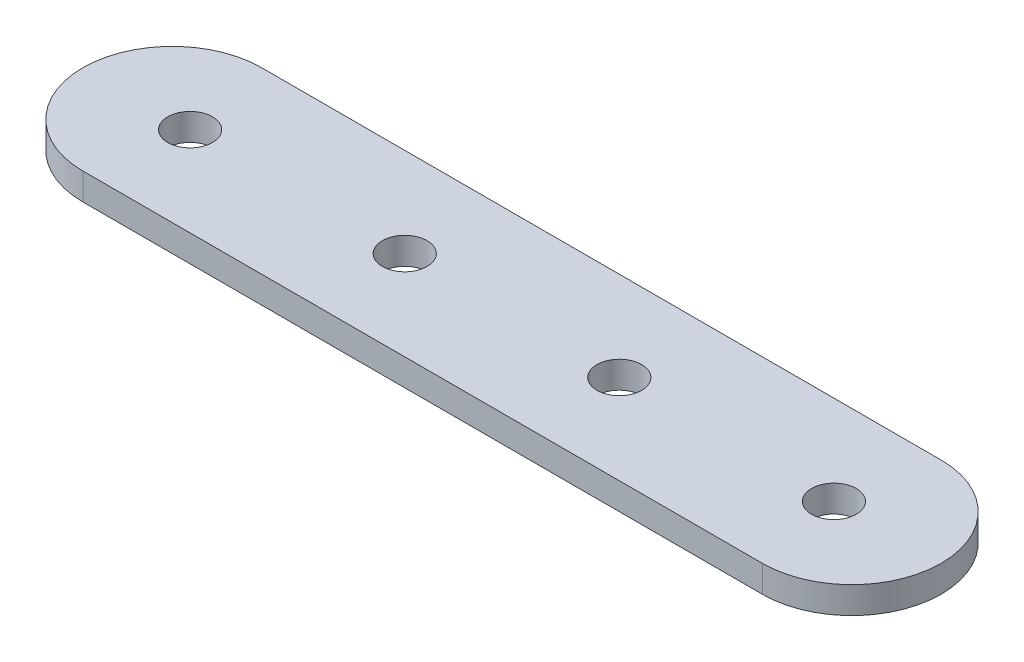
SolidWorks part; units mm, degrees
ref_plane "前视基准面" through (0, 0, 0) normal (0, 0, 1) x (1, 0, 0)
ref_plane "上视基准面" through (0, 0, 0) normal (0, 1, 0) x (1, 0, 0)
ref_plane "右视基准面" through (0, 0, 0) normal (1, 0, 0) x (0, 0, -1)
sketch "草图1" plane through (0, 0, 0) normal (0, 1, 0) x (1, 0, 0)
  line L0 (10, 0) -> (86, 0)
  line L2 (86, 20) -> (10, 20)
  arc A0 (10, 20) -> (10, 0) centre (10, 10) ccw
  arc A1 (86, 0) -> (86, 20) centre (86, 10) ccw
  circle A2 centre (12, 10) radius 2.5
  circle A3 centre (36, 10) radius 2.5
  circle A4 centre (60, 10) radius 2.5
  circle A5 centre (84, 10) radius 2.5
  point P4 (0, 10)
  point P6 (96, 10)
  dimension "D6" = 5
  dimension "D1" = 20
  dimension "D2" = 96
  dimension "D3" = 12
  dimension "D5" = 10
  dimension "D4" = 4
extrude "凸台-拉伸1" add sketch "草图1" along normal blind 3
